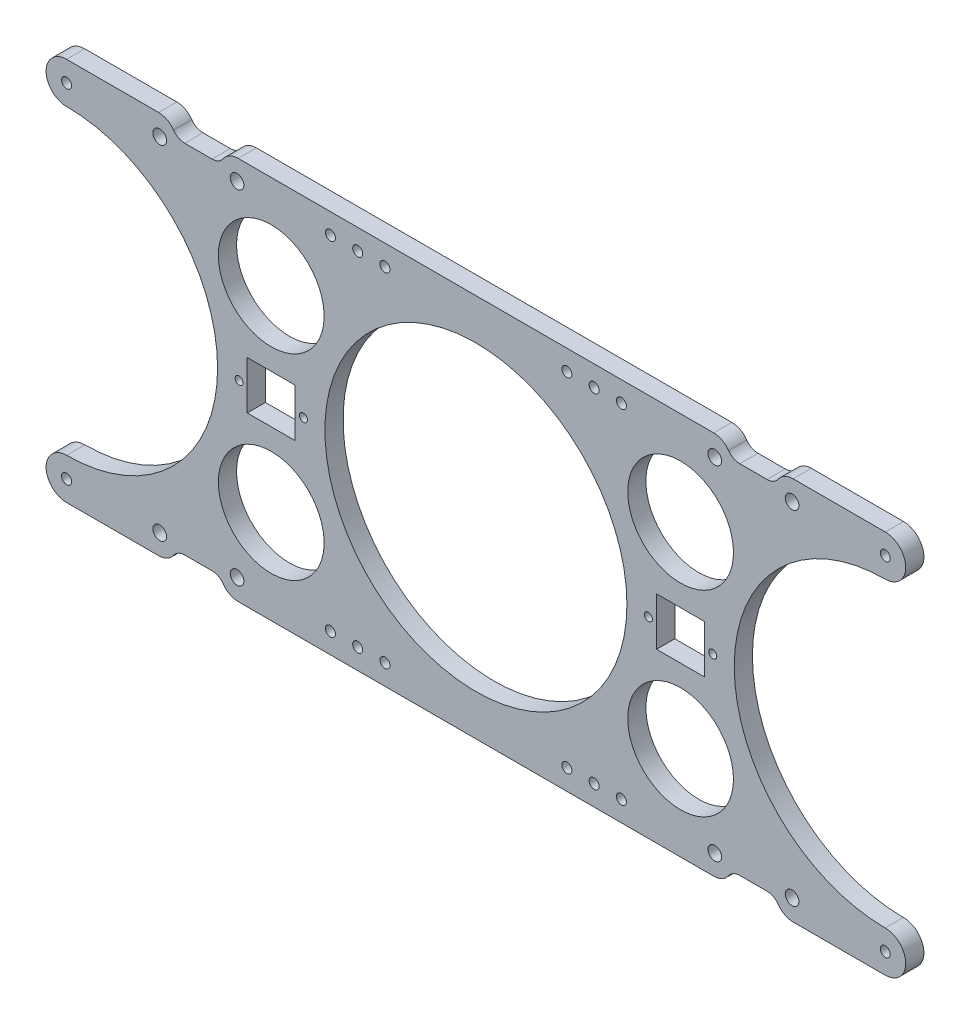
SolidWorks part; units mm, degrees
material "6061 Alloy"
ref_plane "Front Plane" through (0, 0, 0) normal (0, 0, 1) x (1, 0, 0)
ref_plane "Top Plane" through (0, 0, 0) normal (0, 1, 0) x (1, 0, 0)
ref_plane "Right Plane" through (0, 0, 0) normal (1, 0, 0) x (0, 0, -1)
sketch "Sketch1" plane through (0, 0, 0) normal (0, 0, 1) x (1, 0, 0)
  line L0 (0, 0) -> (225.1042, 0) construction
  line L1 (112.5521, -53.975) -> (112.5521, 53.975) construction
  line L2 (0, 83.05) -> (225.1042, 83.05) construction
  line L3 (225.1042, 83.05) -> (225.1042, -83.05) construction
  line L4 (-225.1042, 105.55) -> (-167.6042, 105.55)
  line L5 (-225.1042, -105.55) -> (-167.6042, -105.55)
  line L6 (0, 83.05) -> (0, 0) construction
  line L7 (-99.3521, -13.2) -> (-99.3521, 13.2)
  line L8 (99.3521, -13.2) -> (125.7521, -13.2)
  line L9 (99.3521, -13.2) -> (99.3521, 13.2)
  line L10 (99.3521, 13.2) -> (125.7521, 13.2)
  line L11 (125.7521, -13.2) -> (125.7521, 13.2)
  line L12 (99.3521, -13.2) -> (125.7521, 13.2) construction
  line L13 (99.3521, 13.2) -> (125.7521, -13.2) construction
  line L14 (-99.3521, 13.2) -> (-125.7521, 13.2)
  line L15 (-125.7521, -13.2) -> (-125.7521, 13.2)
  line L16 (-99.3521, -13.2) -> (-125.7521, -13.2)
  line L17 (0, 83.05) -> (0, 98.05) construction
  line L18 (50, 94.3) -> (80, 94.3) construction
  line L19 (80, 94.3) -> (94.2894, 76.5986) construction
  line L20 (225.1042, 0) -> (148.4177, 105.55) construction
  line L21 (225.1042, 0) -> (148.4177, -105.55) construction
  line L38 (-236.3542, 105.55) -> (-236.3542, -105.55) construction
  line L39 (-236.3542, -105.55) -> (-167.6042, -105.55) construction
  line L40 (236.3542, -105.55) -> (236.3542, 105.55) construction
  line L41 (236.3542, 105.55) -> (167.6042, 105.55) construction
  line L42 (-160.1042, 98.05) -> (-145.1042, 98.05)
  line L44 (-152.6042, 98.05) -> (-152.6042, 105.55) construction
  line L45 (-137.6042, 105.55) -> (137.6042, 105.55)
  line L46 (-167.6042, 105.55) -> (-236.3542, 105.55) construction
  line L47 (-160.1042, -98.05) -> (-145.1042, -98.05)
  line L48 (160.1042, -98.05) -> (145.1042, -98.05)
  line L49 (160.1042, 98.05) -> (145.1042, 98.05)
  line L50 (-137.6042, -105.55) -> (137.6042, -105.55) construction
  line L51 (-137.6042, -105.55) -> (137.6042, -105.55)
  line L52 (167.6042, -105.55) -> (225.1042, -105.55)
  line L53 (167.6042, -105.55) -> (236.3542, -105.55) construction
  line L54 (137.6042, 105.55) -> (-137.6042, 105.55) construction
  line L55 (167.6042, 105.55) -> (225.1042, 105.55)
  circle A0 centre (0, 0) radius 83.05
  arc A1 (225.1042, 83.05) -> (225.1042, -83.05) centre (225.1042, 0) ccw
  circle A2 centre (112.5521, 53.975) radius 29.075
  circle A3 centre (112.5521, -53.975) radius 29.075
  arc A4 (225.1042, 83.05) -> (225.1042, 105.55) centre (225.1042, 94.3) ccw
  arc A5 (225.1042, -83.05) -> (225.1042, -105.55) centre (225.1042, -94.3) cw
  circle A6 centre (-112.5521, -53.975) radius 29.075
  arc A7 (-225.1042, -83.05) -> (-225.1042, -105.55) centre (-225.1042, -94.3) ccw
  arc A8 (-225.1042, 83.05) -> (-225.1042, 105.55) centre (-225.1042, 94.3) cw
  circle A9 centre (-112.5521, 53.975) radius 29.075
  arc A10 (-225.1042, 83.05) -> (-225.1042, -83.05) centre (-225.1042, 0) cw
  circle A11 centre (225.1042, 0) radius 94.3 construction
  circle A13 centre (-195.1042, 94.3) radius 2.75 construction
  circle A31 centre (94.8521, 0) radius 2.2
  circle A32 centre (130.2521, 0) radius 2.2
  circle A33 centre (-130.2521, 0) radius 2.2
  circle A34 centre (-94.8521, 0) radius 2.2
  circle A35 centre (130.2521, 0) radius 3.175 construction
  circle A36 centre (225.1042, 0) radius 88.9 construction
  arc A37 (-167.6042, 105.55) -> (-160.1042, 98.05) centre (-160.1042, 105.55) ccw
  arc A38 (-145.1042, 98.05) -> (-137.6042, 105.55) centre (-145.1042, 105.55) ccw
  circle A39 centre (-195.1042, 94.3) radius 7.5 construction
  circle A40 centre (-173.8542, 94.3) radius 3.75
  circle A42 centre (-131.3542, 94.3) radius 3.75
  arc A43 (-145.1042, -98.05) -> (-137.6042, -105.55) centre (-145.1042, -105.55) cw
  arc A44 (-167.6042, -105.55) -> (-160.1042, -98.05) centre (-160.1042, -105.55) cw
  circle A45 centre (-131.3542, -94.3) radius 3.75
  circle A46 centre (-173.8542, -94.3) radius 3.75
  circle A47 centre (131.3542, -94.3) radius 3.75
  arc A48 (145.1042, -98.05) -> (137.6042, -105.55) centre (145.1042, -105.55) ccw
  arc A49 (167.6042, -105.55) -> (160.1042, -98.05) centre (160.1042, -105.55) ccw
  circle A50 centre (173.8542, -94.3) radius 3.75
  circle A51 centre (131.3542, 94.3) radius 3.75
  arc A52 (145.1042, 98.05) -> (137.6042, 105.55) centre (145.1042, 105.55) cw
  arc A53 (167.6042, 105.55) -> (160.1042, 98.05) centre (160.1042, 105.55) cw
  circle A54 centre (173.8542, 94.3) radius 3.75
  point P9 (112.5521, 0)
  point P10 (112.5521, 0)
  point P24 (0, -98.05)
  point P25 (0, 98.05)
  point P30 (112.5521, 0)
  point P31 (225.1042, 94.3)
  point P32 (225.1042, -94.3)
  point P33 (-225.1042, -94.3)
  point P34 (-225.1042, 94.3)
  point P46 (65, 94.3)
  point P48 (-80, 94.3)
  point P49 (-65, 94.3)
  point P50 (50, 94.3)
  point P51 (80, 94.3)
  point P52 (-50, 94.3)
  point P54 (80, -94.3)
  point P55 (65, -94.3)
  point P56 (50, -94.3)
  point P57 (-50, -94.3)
  point P58 (-65, -94.3)
  point P59 (-80, -94.3)
  point P63 (195.1042, -94.3)
  point P66 (-195.1042, -94.3)
  point P67 (-195.1042, 94.3)
  point P70 (195.1042, 94.3)
  dimension "D1" = 166.1
  dimension "D3" = 58.15
  dimension "D10" = 5.5
  dimension "D16" = 4.4
  dimension "D20" = 6.35
  dimension "D21" = 177.8
  dimension "D11" = 7.5
  dimension "D14" = 15
  dimension "D13" = 7.5
  dimension "D2" = 12.7
  dimension "D4" = 22.5
  dimension "D5" = 26.4
  dimension "D7" = 50
  dimension "D6" = 15
  dimension "D8" = 36
  dimension "D17" = 4.5
  dimension "D18" = 211.1
  dimension "D19" = 472.7085
  dimension "D12" = 15
  dimension "D15" = 20
  dimension "D22" = 10
  dimension "D9" = 30
extrude "Boss-Extrude1" add sketch "Sketch1" along normal mid plane 10
sketch "Sketch2" plane through (0, 0, 0) normal (0, 1, 0) x (1, 0, 0)
  line L0 (-196.3542, 5) -> (-196.3542, -5) construction
  line L2 (-167.6042, 5) -> (-225.1042, 5) construction
  line L3 (-167.6042, -5) -> (-225.1042, -5) construction
  line L4 (0, 0) -> (110.0348, 0) construction
  line L5 (110.0348, 5) -> (110.0348, -5) construction
hole_wizard "M5 Clearance Hole1" positions "Sketch3" profile "Sketch4" hole size "M5" standard "ANSI Metric" end condition through all
sketch "Sketch3" plane through (0, 0, 5) normal (0, 0, 1) x (1, 0, 0)
  line L0 (-3000, 0) -> (3000, 0) construction
  line L1 (0, -1000) -> (0, 49000) construction
  point P0 (-80, 94.3)
  point P3 (-65, 94.3)
  point P6 (-50, 94.3)
  point P9 (50, 94.3)
  point P12 (65, 94.3)
  point P15 (80, 94.3)
  point P18 (-80, -94.3)
  point P21 (-65, -94.3)
  point P24 (-50, -94.3)
  point P27 (50, -94.3)
  point P30 (65, -94.3)
  point P33 (80, -94.3)
  point P78 (0, 0)
  point P96 (-225.1042, 94.3)
  point P105 (225.1042, 94.3)
  point P108 (225.1042, -94.3)
  point P111 (-225.1042, -94.3)
sketch "Sketch4" plane through (-80, 94.3, 5) normal (1, 0, 0) x (0, -1, 0)
  line L0 (0, 0) -> (0, 10)
  line L1 (0, 10) -> (2.75, 10)
  line L2 (2.75, 10) -> (2.75, 0)
  line L5 (2.75, 0) -> (0, 0)
  line L11 (0, -6.35) -> (0, 107.95) construction
  dimension "Thru Hole Dia." = 5.5
  dimension "Thru Hole Depth" = 10
fillet "Fillet1" radius 10 8 edges at (167.6042, 105.55, 0) (137.6042, 105.55, 0) (167.6042, -105.55, 0) (137.6042, -105.55, 0) (-137.6042, -105.55, 0) (-167.6042, -105.55, 0) (-137.6042, 105.55, 0) (-167.6042, 105.55, 0)
equation "\"D1@Sketch1\"=152.40 + (6.35*2) + 1"
